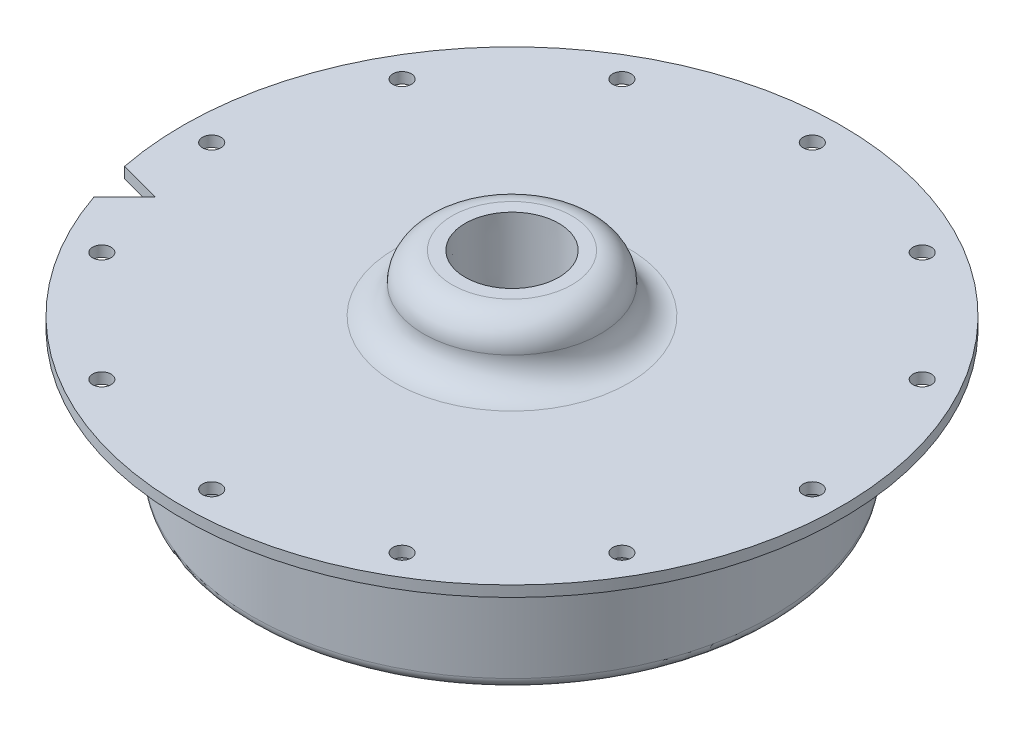
SolidWorks part; units mm, degrees
material "6063-T6"
ref_plane "Front Plane" through (0, 0, 0) normal (0, 0, 1) x (1, 0, 0)
ref_plane "Top Plane" through (0, 0, 0) normal (0, 1, 0) x (1, 0, 0)
ref_plane "Right Plane" through (0, 0, 0) normal (1, 0, 0) x (0, 0, -1)
ref_axis "Axis1" through (0, 55, 0) along (0, -1, 0)
sketch "Sketch1" plane through (0, 0, 0) normal (0, 0, 1) x (1, 0, 0)
  line L0 (-48.26, 0) -> (-39.6875, 0)
  line L1 (0, 55) -> (0, -55) construction
  line L2 (-48.26, 0) -> (-48.26, 1.5875)
  line L3 (-5.588, 9.906) -> (-8.763, 9.906)
  line L5 (-5.588, 9.906) -> (-5.588, 0)
  line L6 (-5.588, 0) -> (0, 0) construction
  line L7 (-48.26, 0) -> (-48.26, 1.5875) construction
  line L8 (-5.588, 1.5875) -> (-5.588, 0) construction
  line L9 (-38.1, -1.5875) -> (-38.1, -17.4625)
  line L11 (-34.925, -17.4625) -> (-34.925, -3.175)
  line L12 (-31.75, 0) -> (-5.588, 0)
  line L13 (0, -201000) -> (0, 249000) construction
  line L14 (-48.26, 1.5875) -> (-17.0815, 1.5875)
  arc A0 (-34.925, -3.175) -> (-31.75, 0) centre (-31.75, -3.175) cw
  arc A1 (-38.1, -1.5875) -> (-39.6875, 0) centre (-39.6875, -1.5875) ccw
  arc A2 (-17.0815, 1.5875) -> (-12.9223, 5.7467) centre (-17.0815, 5.7467) ccw
  arc A3 (-8.763, 9.906) -> (-12.9223, 5.7467) centre (-8.763, 5.7467) ccw
  arc A4 (-38.1, -17.4625) -> (-34.925, -17.4625) centre (-36.5125, -17.4625) ccw
  point P18 (-34.925, 0)
  dimension "D4" = 3.175
  dimension "D5" = 1.5875
  dimension "D1" = 3.175
  dimension "D2" = 38.1
  dimension "D3" = 17.4625
  dimension "D6" = 1.5875
  dimension "D7" = 3.175
  dimension "D8" = 9.906
revolve "Revolve1" add sketch "Sketch1" angle 360 about axis through (0, 55, 0) along (0, -1, 0)
ref_plane "Hole Location Plane" through (0, 3.175, 0) normal (0, 1, 0) x (1, 0, 0)
sketch "Hole Location" plane through (0, 3.175, 0) normal (0, 1, 0) x (1, 0, 0)
  line L0 (0, 0) -> (-43.9737, 0) construction
  circle A0 centre (0, 0) radius 43.9737 construction
  dimension "D1" = 87.9475
hole_wizard "#36 (0.1065) Diameter Hole1" positions "Sketch2" profile "Sketch3" hole size "#36" standard "ANSI Inch" end condition through all
sketch "Sketch2" plane through (0, 1.5875, 0) normal (0, 1, 0) x (1, 0, 0)
  point P0 (-43.9737, 0)
sketch "Sketch3" plane through (-43.9737, 1.5875, 0) normal (1, 0, 0) x (0, 0, 1)
  line L0 (0, 0) -> (0, 20.6375)
  line L1 (0, 20.6375) -> (1.3525, 20.6375)
  line L2 (1.3525, 20.6375) -> (1.3525, 0)
  line L5 (1.3525, 0) -> (0, 0)
  line L11 (0, -6.35) -> (0, 107.95) construction
  dimension "Thru Hole Dia." = 2.7051
  dimension "Thru Hole Depth" = 20.6375
pattern_circular "CirPattern1" count 12 over 360 about axis through (0, 0, 0) along (0, 1, 0) of "#36 (0.1065) Diameter Hole1"
hole_wizard "1/4 NPT Tapped Hole1" positions "Sketch4" profile "Sketch5" size "1/4" standard "ANSI Inch" end condition through all
sketch "Sketch4" plane through (0, 9.906, 0) normal (0, 1, 0) x (1, 0, 0)
  point P0 (0, 0)
sketch "Sketch5" plane through (0, 9.906, 0) normal (1, 0, 0) x (0, 0, 1)
  line L0 (0, 0) -> (0, 28.956)
  line L1 (0, 28.956) -> (5.5626, 28.956)
  line L2 (-6.558, 9.906) -> (-6.8546, 0) construction
  line L3 (5.5626, 28.956) -> (5.5626, 9.906)
  line L4 (5.5626, 9.906) -> (6.558, 9.906)
  line L5 (6.558, 9.906) -> (6.8546, 0)
  line L7 (6.8546, 0) -> (0, 0)
  line L8 (0, -6.35) -> (0, 107.95) construction
  line L11 (-5.5626, 9.906) -> (-6.558, 9.906) construction
  dimension "Thru Tap Drill Dia." = 11.1252
  dimension "Thru Tap Drill Depth" = 28.956
  dimension "Thread Dia." = 13.7092
  dimension "Thread Angle" = 3.43
  dimension "Thread Depth" = 9.906
sketch "Sketch6" plane through (0, 1.5875, 0) normal (0, 1, 0) x (1, 0, 0)
  line L0 (0, 0) -> (-46.6156, -12.4906) construction
  line L1 (0, 0) -> (-43.9737, 0) construction
  line L2 (-45.6928, -15.5304) -> (-41.2027, -11.0402)
  line L3 (-41.2027, -11.0402) -> (-47.3363, -9.3967)
  circle A0 centre (0, 0) radius 48.26 construction
  arc A1 (-45.6928, -15.5304) -> (-47.3363, -9.3967) centre (0, 0) cw
  circle M16 centre (0, 0) radius 48.26
  dimension "D1" = 15
  dimension "D2" = 60
  dimension "D3" = 6.35
extrude "Cut-Extrude1" cut sketch "Sketch6" against normal up to surface (1.5875 mm away) contours L2 L0 A1 | L0 L3 M16 up to face at (-38.0824, 0, -23.3394)
equation "\"D1@Hole Location\"=\"TANK DIAMETER@Cryo Tank.Assembly\"+\"GASKET SEAT THICKNESS@Cryo Tank.Assembly\"+\"LINER THICKNESS@Cryo Tank.Assembly\""
equation "\"D2@Sketch1\"=\"TANK DIAMETER@Cryo Tank.Assembly\"/2"
equation "\"D3@Sketch1\"=0.5+0.125+0.0625"
